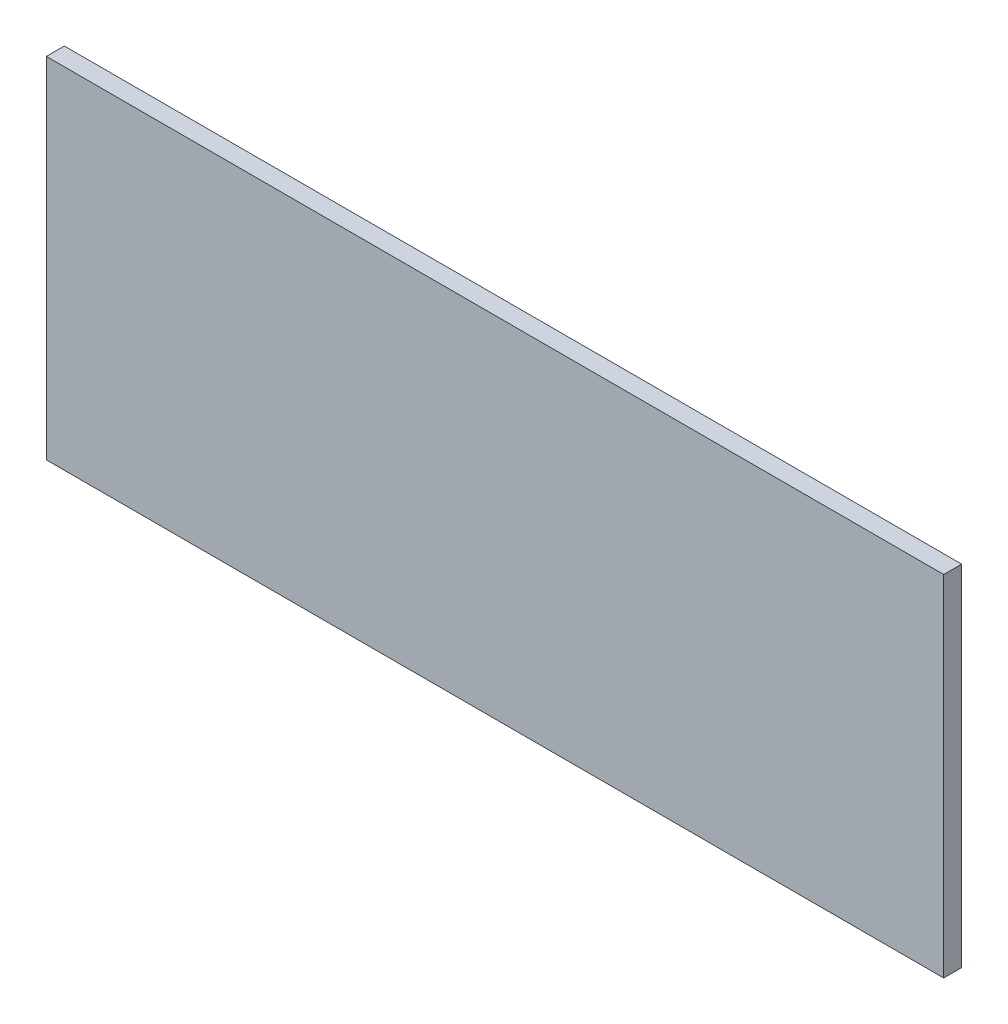
SolidWorks part; units mm, degrees
ref_plane "Front Plane" through (0, 0, 0) normal (0, 0, 1) x (1, 0, 0)
ref_plane "Top Plane" through (0, 0, 0) normal (0, 1, 0) x (1, 0, 0)
ref_plane "Right Plane" through (0, 0, 0) normal (1, 0, 0) x (0, 0, -1)
sketch "Sketch1" plane through (0, 0, 0) normal (0, 0, 1) x (1, 0, 0)
  line L0 (0, 0) -> (249.6, 0)
  line L5 (0, 0) -> (0, -97.1922)
  line L6 (249.6, 0) -> (249.6, -97.1922)
  line L7 (0, -97.1922) -> (249.6, -97.1922)
  point P0 (0, 0)
  dimension "D1" = 249.6
  dimension "D2" = 97.1922
extrude "Boss-Extrude1" add sketch "Sketch1" along normal blind 5
